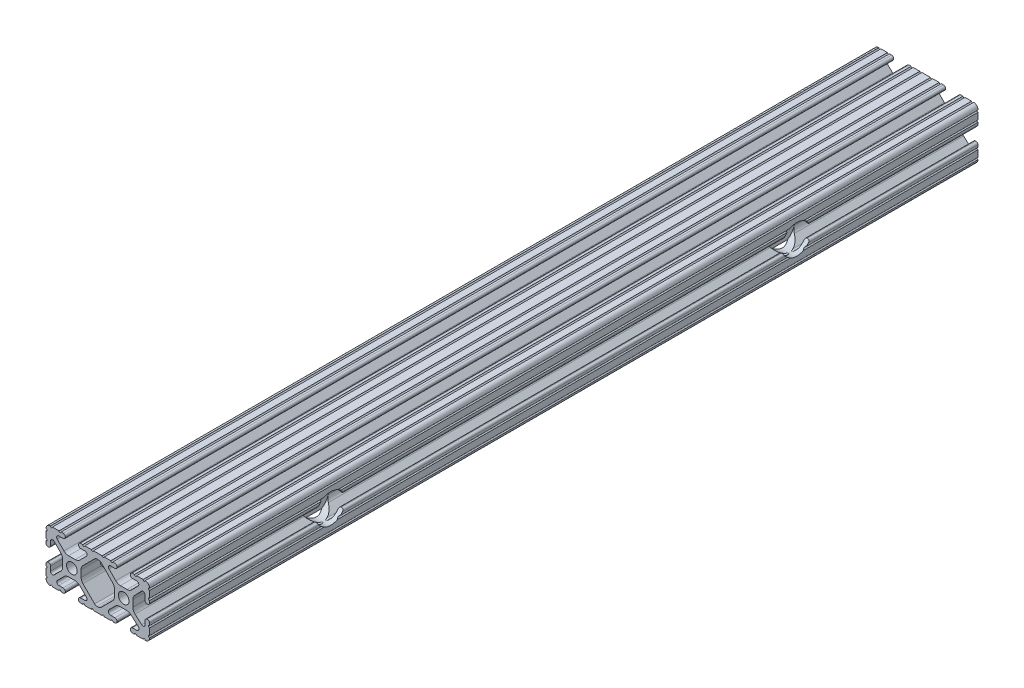
SolidWorks part; units mm, degrees
ref_plane "Front Plane" through (0, 0, 0) normal (0, 0, 1) x (1, 0, 0)
ref_plane "Top Plane" through (0, 0, 0) normal (0, 1, 0) x (1, 0, 0)
ref_plane "Right Plane" through (0, 0, 0) normal (1, 0, 0) x (0, 0, -1)
sketch "Sketch1" plane through (0, 0, 0) normal (0, 0, 1) x (1, 0, 0)
  line L0 (-7.2595, -3.8694) -> (-1.5457, -9.5728)
  line L1 (-8.1915, 1.6223) -> (-8.1915, -1.6223)
  line L2 (-1.504, 9.5765) -> (-7.252, 3.8768)
  line L3 (0.5515, 10.033) -> (-0.3952, 10.033)
  line L4 (7.2829, 3.8459) -> (1.6756, 9.5611)
  line L5 (8.1915, -1.6223) -> (8.1915, 1.6223)
  line L6 (1.5457, -9.5728) -> (7.2595, -3.8694)
  line L7 (-0.4332, -10.033) -> (0.4332, -10.033)
  line L8 (18.0171, 12.7) -> (16.9875, 12.7)
  line L9 (15.9385, 11.651) -> (15.9385, 11.5392)
  line L10 (16.9875, 10.4902) -> (19.1164, 10.4902)
  line L11 (19.8441, 8.7652) -> (16.619, 5.4551)
  line L12 (14.3449, 4.4958) -> (11.0833, 4.4958)
  line L13 (8.817, 5.4472) -> (5.5642, 8.7627)
  line L14 (6.2894, 10.4902) -> (8.4125, 10.4902)
  line L15 (9.4615, 11.5392) -> (9.4615, 11.651)
  line L16 (8.4125, 12.7) -> (7.3829, 12.7)
  line L17 (6.3669, 12.7) -> (3.1496, 12.7)
  line L18 (2.1336, 12.7) -> (-2.1336, 12.7)
  line L19 (-3.1496, 12.7) -> (-6.3669, 12.7)
  line L20 (-7.3829, 12.7) -> (-8.4125, 12.7)
  line L21 (-9.4615, 11.651) -> (-9.4615, 11.5392)
  line L22 (-8.4125, 10.4902) -> (-6.2836, 10.4902)
  line L23 (-5.5326, 8.6661) -> (-8.81, 5.4163)
  line L24 (-11.0455, 4.4958) -> (-14.3545, 4.4958)
  line L25 (-16.59, 5.4163) -> (-19.8674, 8.6661)
  line L26 (-19.1164, 10.4902) -> (-16.9875, 10.4902)
  line L27 (-15.9385, 11.5392) -> (-15.9385, 11.651)
  line L28 (-16.9875, 12.7) -> (-18.0171, 12.7)
  line L29 (-19.0331, 12.7) -> (-22.2504, 12.7)
  line L30 (-25.4, 9.5504) -> (-25.4, 6.3331)
  line L31 (-25.4, 5.3171) -> (-25.4, 4.2375)
  line L32 (-24.401, 3.2385) -> (-24.2392, 3.2385)
  line L33 (-23.1902, 4.2875) -> (-23.1902, 6.3347)
  line L34 (-21.434, 7.0665) -> (-18.148, 3.8082)
  line L35 (-17.2085, 1.5536) -> (-17.2085, -1.6952)
  line L36 (-18.1405, -3.9423) -> (-21.4316, -7.2274)
  line L37 (-23.1902, -6.498) -> (-23.1902, -4.2875)
  line L38 (-24.2392, -3.2385) -> (-24.351, -3.2385)
  line L39 (-25.4, -4.2875) -> (-25.4, -5.3171)
  line L40 (-25.4, -6.3331) -> (-25.4, -9.5504)
  line L41 (-22.2504, -12.7) -> (-19.0331, -12.7)
  line L42 (-18.0171, -12.7) -> (-16.9875, -12.7)
  line L43 (-15.9384, -11.651) -> (-15.9384, -11.5392)
  line L44 (-16.9875, -10.4902) -> (-19.1164, -10.4902)
  line L45 (-19.8341, -8.7551) -> (-16.4966, -5.4237)
  line L46 (-14.2536, -4.4958) -> (-11.1464, -4.4958)
  line L47 (-8.9034, -5.4237) -> (-5.5659, -8.7551)
  line L48 (-6.2836, -10.4902) -> (-8.4125, -10.4902)
  line L49 (-9.4616, -11.5392) -> (-9.4616, -11.651)
  line L50 (-8.4125, -12.7) -> (-7.3829, -12.7)
  line L51 (-6.3669, -12.7) -> (-3.1496, -12.7)
  line L52 (-2.1336, -12.7) -> (2.1336, -12.7)
  line L53 (3.1496, -12.7) -> (6.3669, -12.7)
  line L54 (7.3829, -12.7) -> (8.4125, -12.7)
  line L55 (9.4616, -11.651) -> (9.4616, -11.5392)
  line L56 (8.4125, -10.4902) -> (6.2894, -10.4902)
  line L57 (5.4807, -8.5353) -> (8.5979, -5.4237)
  line L58 (10.8409, -4.4958) -> (14.1026, -4.4958)
  line L59 (16.1879, -5.2766) -> (19.8682, -8.4822)
  line L60 (19.1164, -10.4902) -> (16.9875, -10.4902)
  line L61 (15.9384, -11.5392) -> (15.9384, -11.651)
  line L62 (16.9875, -12.7) -> (18.0171, -12.7)
  line L63 (19.0331, -12.7) -> (22.2504, -12.7)
  line L64 (25.4, -9.5504) -> (25.4, -6.3331)
  line L65 (25.4, -5.3171) -> (25.4, -4.2375)
  line L66 (24.401, -3.2385) -> (24.1892, -3.2385)
  line L67 (23.1902, -4.2375) -> (23.1902, -6.1559)
  line L68 (21.584, -6.8869) -> (18.2982, -4.025)
  line L69 (17.2085, -1.6308) -> (17.2085, 1.6308)
  line L70 (18.1094, 3.8465) -> (21.5263, 7.3534)
  line L71 (23.1902, 6.6769) -> (23.1902, 4.2375)
  line L72 (24.1892, 3.2385) -> (24.401, 3.2385)
  line L73 (25.4, 4.2375) -> (25.4, 5.3171)
  line L74 (25.4, 6.3332) -> (25.4, 9.5504)
  line L75 (22.2504, 12.7) -> (19.0331, 12.7)
  circle A0 centre (-12.7, 0) radius 2.6035
  circle A1 centre (12.7, 0) radius 2.6035
  arc A2 (-1.5457, -9.5728) -> (-0.4332, -10.033) centre (-0.4332, -8.4582) ccw
  arc A3 (-8.1915, -1.6223) -> (-7.2595, -3.8694) centre (-5.0165, -1.6223) ccw
  arc A4 (-7.252, 3.8768) -> (-8.1915, 1.6223) centre (-5.0165, 1.6223) ccw
  arc A5 (-0.3952, 10.033) -> (-1.504, 9.5765) centre (-0.3952, 8.4582) ccw
  arc A6 (1.6756, 9.5611) -> (0.5515, 10.033) centre (0.5515, 8.4582) ccw
  arc A7 (8.1915, 1.6223) -> (7.2829, 3.8459) centre (5.0165, 1.6223) ccw
  arc A8 (7.2595, -3.8694) -> (8.1915, -1.6223) centre (5.0165, -1.6223) ccw
  arc A9 (0.4332, -10.033) -> (1.5457, -9.5728) centre (0.4332, -8.4582) ccw
  arc A10 (18.0171, 12.7) -> (19.0331, 12.7) centre (18.5251, 12.7) ccw
  arc A11 (16.9875, 12.7) -> (15.9385, 11.651) centre (16.9875, 11.651) ccw
  arc A12 (15.9385, 11.5392) -> (16.9875, 10.4902) centre (16.9875, 11.5392) ccw
  arc A13 (19.8441, 8.7652) -> (19.1164, 10.4902) centre (19.1164, 9.4742) ccw
  arc A14 (14.3449, 4.4958) -> (16.619, 5.4551) centre (14.3449, 7.6708) ccw
  arc A15 (8.817, 5.4472) -> (11.0833, 4.4958) centre (11.0833, 7.6708) ccw
  arc A16 (6.2894, 10.4902) -> (5.5642, 8.7627) centre (6.2894, 9.4742) ccw
  arc A17 (8.4125, 10.4902) -> (9.4615, 11.5392) centre (8.4125, 11.5392) ccw
  arc A18 (9.4615, 11.651) -> (8.4125, 12.7) centre (8.4125, 11.651) ccw
  arc A19 (6.3669, 12.7) -> (7.3829, 12.7) centre (6.8749, 12.7) ccw
  arc A20 (2.1336, 12.7) -> (3.1496, 12.7) centre (2.6416, 12.7) ccw
  arc A21 (-3.1496, 12.7) -> (-2.1336, 12.7) centre (-2.6416, 12.7) ccw
  arc A22 (-7.3829, 12.7) -> (-6.3669, 12.7) centre (-6.8749, 12.7) ccw
  arc A23 (-8.4125, 12.7) -> (-9.4615, 11.651) centre (-8.4125, 11.651) ccw
  arc A24 (-9.4615, 11.5392) -> (-8.4125, 10.4902) centre (-8.4125, 11.5392) ccw
  arc A25 (-5.5326, 8.6661) -> (-6.2836, 10.4902) centre (-6.2836, 9.4235) ccw
  arc A26 (-11.0455, 4.4958) -> (-8.81, 5.4163) centre (-11.0455, 7.6708) ccw
  arc A27 (-16.59, 5.4163) -> (-14.3545, 4.4958) centre (-14.3545, 7.6708) ccw
  arc A28 (-19.1164, 10.4902) -> (-19.8674, 8.6661) centre (-19.1164, 9.4235) ccw
  arc A29 (-16.9875, 10.4902) -> (-15.9385, 11.5392) centre (-16.9875, 11.5392) ccw
  arc A30 (-15.9385, 11.651) -> (-16.9875, 12.7) centre (-16.9875, 11.651) ccw
  arc A31 (-19.0331, 12.7) -> (-18.0171, 12.7) centre (-18.5251, 12.7) ccw
  arc A32 (-23.2664, 12.6998) -> (-22.2504, 12.7) centre (-22.7584, 12.7) ccw
  arc A33 (-23.2664, 12.6998) -> (-25.3998, 10.5664) centre (-23.2918, 10.5918) ccw
  arc A34 (-25.4, 9.5504) -> (-25.3998, 10.5664) centre (-25.4, 10.0584) ccw
  arc A35 (-25.4, 5.3171) -> (-25.4, 6.3331) centre (-25.4, 5.8251) ccw
  arc A36 (-25.4, 4.2375) -> (-24.401, 3.2385) centre (-24.401, 4.2375) ccw
  arc A37 (-24.2392, 3.2385) -> (-23.1902, 4.2875) centre (-24.2392, 4.2875) ccw
  arc A38 (-21.434, 7.0665) -> (-23.1902, 6.3347) centre (-22.1596, 6.3347) ccw
  arc A39 (-17.2085, 1.5536) -> (-18.148, 3.8082) centre (-20.3835, 1.5536) ccw
  arc A40 (-18.1405, -3.9423) -> (-17.2085, -1.6952) centre (-20.3835, -1.6952) ccw
  arc A41 (-23.1902, -6.498) -> (-21.4316, -7.2274) centre (-22.1596, -6.498) ccw
  arc A42 (-23.1902, -4.2875) -> (-24.2392, -3.2385) centre (-24.2392, -4.2875) ccw
  arc A43 (-24.351, -3.2385) -> (-25.4, -4.2875) centre (-24.351, -4.2875) ccw
  arc A44 (-25.4, -6.3331) -> (-25.4, -5.3171) centre (-25.4, -5.8251) ccw
  arc A45 (-25.3998, -10.5664) -> (-25.4, -9.5504) centre (-25.4, -10.0584) ccw
  arc A46 (-25.3998, -10.5664) -> (-23.2664, -12.6998) centre (-23.2918, -10.5918) ccw
  arc A47 (-22.2504, -12.7) -> (-23.2664, -12.6998) centre (-22.7584, -12.7) ccw
  arc A48 (-18.0171, -12.7) -> (-19.0331, -12.7) centre (-18.5251, -12.7) ccw
  arc A49 (-16.9875, -12.7) -> (-15.9384, -11.651) centre (-16.9875, -11.651) ccw
  arc A50 (-15.9384, -11.5392) -> (-16.9875, -10.4902) centre (-16.9875, -11.5392) ccw
  arc A51 (-19.8341, -8.7551) -> (-19.1164, -10.4902) centre (-19.1164, -9.4742) ccw
  arc A52 (-14.2536, -4.4958) -> (-16.4966, -5.4237) centre (-14.2536, -7.6708) ccw
  arc A53 (-8.9034, -5.4237) -> (-11.1464, -4.4958) centre (-11.1464, -7.6708) ccw
  arc A54 (-6.2836, -10.4902) -> (-5.5659, -8.7551) centre (-6.2836, -9.4742) ccw
  arc A55 (-8.4125, -10.4902) -> (-9.4616, -11.5392) centre (-8.4125, -11.5392) ccw
  arc A56 (-9.4616, -11.651) -> (-8.4125, -12.7) centre (-8.4125, -11.651) ccw
  arc A57 (-6.3669, -12.7) -> (-7.3829, -12.7) centre (-6.8749, -12.7) ccw
  arc A58 (-2.1336, -12.7) -> (-3.1496, -12.7) centre (-2.6416, -12.7) ccw
  arc A59 (3.1496, -12.7) -> (2.1336, -12.7) centre (2.6416, -12.7) ccw
  arc A60 (7.3829, -12.7) -> (6.3669, -12.7) centre (6.8749, -12.7) ccw
  arc A61 (8.4125, -12.7) -> (9.4616, -11.651) centre (8.4125, -11.651) ccw
  arc A62 (9.4616, -11.5392) -> (8.4125, -10.4902) centre (8.4125, -11.5392) ccw
  arc A63 (5.4807, -8.5353) -> (6.2894, -10.4902) centre (6.2894, -9.3455) ccw
  arc A64 (10.8409, -4.4958) -> (8.5979, -5.4237) centre (10.8409, -7.6708) ccw
  arc A65 (16.1879, -5.2766) -> (14.1026, -4.4958) centre (14.1026, -7.6708) ccw
  arc A66 (19.1164, -10.4902) -> (19.8682, -8.4822) centre (19.1164, -9.3455) ccw
  arc A67 (16.9875, -10.4902) -> (15.9384, -11.5392) centre (16.9875, -11.5392) ccw
  arc A68 (15.9384, -11.651) -> (16.9875, -12.7) centre (16.9875, -11.651) ccw
  arc A69 (19.0331, -12.7) -> (18.0171, -12.7) centre (18.5251, -12.7) ccw
  arc A70 (23.2664, -12.6998) -> (22.2504, -12.7) centre (22.7584, -12.7) ccw
  arc A71 (23.2664, -12.6998) -> (25.3998, -10.5664) centre (23.2918, -10.5918) ccw
  arc A72 (25.4, -9.5504) -> (25.3998, -10.5664) centre (25.4, -10.0584) ccw
  arc A73 (25.4, -5.3171) -> (25.4, -6.3331) centre (25.4, -5.8251) ccw
  arc A74 (25.4, -4.2375) -> (24.401, -3.2385) centre (24.401, -4.2375) ccw
  arc A75 (24.1892, -3.2385) -> (23.1902, -4.2375) centre (24.1892, -4.2375) ccw
  arc A76 (21.584, -6.8869) -> (23.1902, -6.1559) centre (22.2207, -6.1559) ccw
  arc A77 (17.2085, -1.6308) -> (18.2982, -4.025) centre (20.3835, -1.6308) ccw
  arc A78 (18.1094, 3.8465) -> (17.2085, 1.6308) centre (20.3835, 1.6308) ccw
  arc A79 (23.1902, 6.6769) -> (21.5263, 7.3534) centre (22.2207, 6.6769) ccw
  arc A80 (23.1902, 4.2375) -> (24.1892, 3.2385) centre (24.1892, 4.2375) ccw
  arc A81 (24.401, 3.2385) -> (25.4, 4.2375) centre (24.401, 4.2375) ccw
  arc A82 (25.4, 6.3332) -> (25.4, 5.3171) centre (25.4, 5.8251) ccw
  arc A83 (25.3998, 10.5664) -> (25.4, 9.5504) centre (25.4, 10.0584) ccw
  arc A84 (25.3998, 10.5664) -> (23.2664, 12.6998) centre (23.2918, 10.5918) ccw
  arc A85 (22.2504, 12.7) -> (23.2664, 12.6998) centre (22.7584, 12.7) ccw
  point P248 (0, 10.033)
extrude "Boss-Extrude1" add sketch "Sketch1" along normal mid plane 406.4
hole_wizard "CBORE for 1/4 Binding Head Machine Screw1" positions "Sketch4" profile "Sketch6" counterbore size "1/4" standard "ANSI Inch" end condition through all
sketch "Sketch4" plane through (25.4, 0, 0) normal (1, 0, 0) x (0, 0, -1)
  line L0 (-114.3, 0) -> (114.3, 0) construction
  point P0 (-114.3, 0)
  point P2 (114.3, 0)
  point P9 (0, 0)
  dimension "D1" = 228.6
sketch "Sketch6" plane through (25.4, 0, 114.3) normal (0, 1, 0) x (0, 0, -1)
  line L0 (0, 0) -> (0, 50.8)
  line L1 (0, 50.8) -> (3.3782, 50.8)
  line L3 (3.3782, 50.8) -> (3.3782, 8.255)
  line L4 (3.3782, 8.255) -> (7.1437, 8.255)
  line L5 (7.1437, 8.255) -> (7.1437, 0)
  line L7 (7.1437, 0) -> (0, 0)
  line L11 (0, -6.35) -> (0, 107.95) construction
  dimension "Thru Hole Dia." = 6.7564
  dimension "Thru Hole Depth" = 50.8
  dimension "C'Bore Dia." = 14.2875
  dimension "C'Bore Depth" = 8.255
hole_wizard "1/4 (0.25) Diameter Hole1" positions "Sketch7" profile "Sketch9" hole size "1/4" standard "ANSI Inch" end condition through all
sketch "Sketch7" plane through (25.4, 0, 0) normal (1, 0, 0) x (0, 0, -1)
  line L0 (-76.2, 0) -> (76.2, 0) construction
  point P0 (-76.2, 0)
  point P2 (76.2, 0)
  point P10 (0, 0)
  dimension "D1" = 152.4
sketch "Sketch9" plane through (25.4, 0, 76.2) normal (0, 1, 0) x (0, 0, -1)
  line L0 (0, 0) -> (0, 50.8)
  line L1 (0, 50.8) -> (3.175, 50.8)
  line L2 (3.175, 50.8) -> (3.175, 0)
  line L5 (3.175, 0) -> (0, 0)
  line L11 (0, -6.35) -> (0, 107.95) construction
  dimension "Thru Hole Dia." = 6.35
  dimension "Thru Hole Depth" = 50.8
sketch "Sketch10" plane through (17.2085, 0, 0) normal (1, 0, 0) x (0, 0, -1)
  line L0 (-203.2, -1.6308) -> (-203.2, 1.6308) construction
  line L1 (0, 0) -> (0, 31.2314) construction
  circle A0 centre (-190.5, 0) radius 3.175
  circle A1 centre (190.5, 0) radius 3.175
  dimension "D1" = 6.35
  dimension "D2" = 12.7
extrude "Cut-Extrude1" cut sketch "Sketch10" against normal through all both and the other way through all
